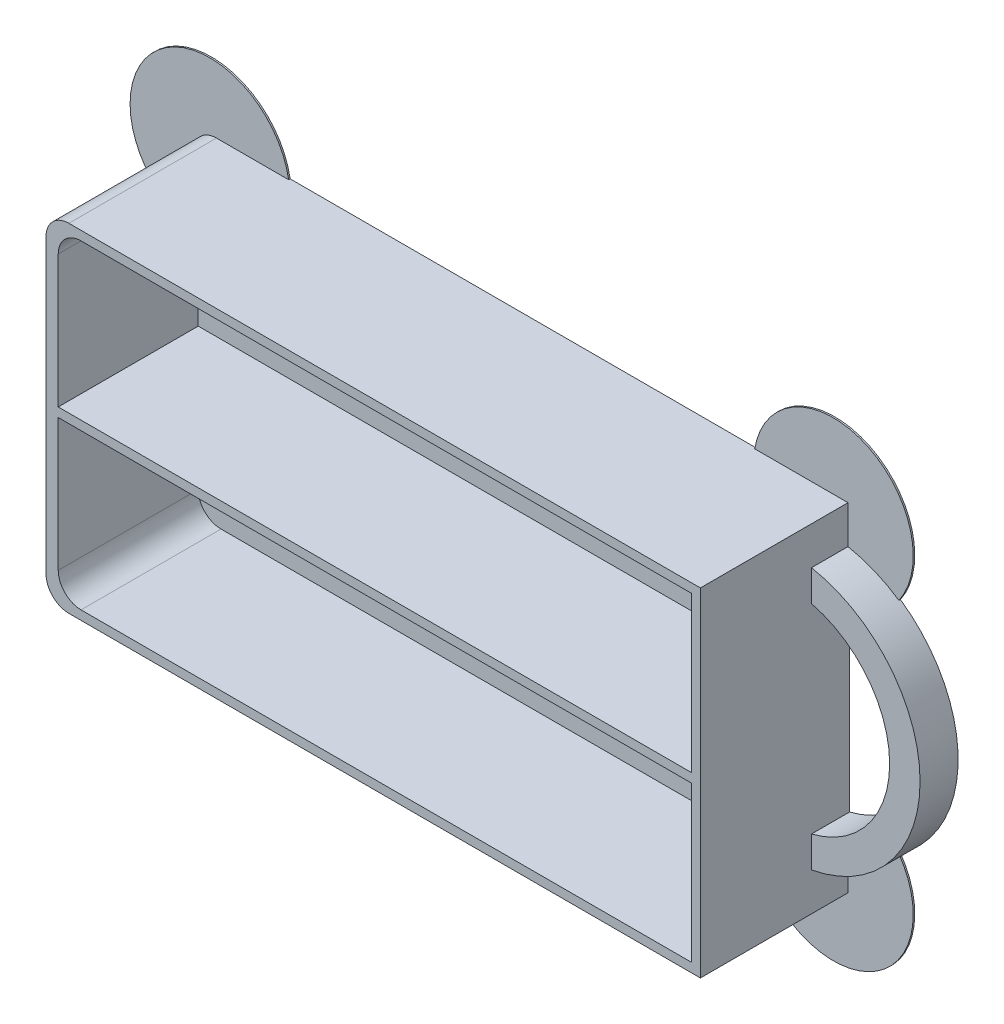
SolidWorks part; units mm, degrees
ref_plane "Спереди" through (0, 0, 0) normal (0, 0, 1) x (1, 0, 0)
ref_plane "Сверху" through (0, 0, 0) normal (0, 1, 0) x (1, 0, 0)
ref_plane "Справа" through (0, 0, 0) normal (1, 0, 0) x (0, 0, -1)
other "Configuration Table"
sketch "Эскиз1" plane through (0, 0, 0) normal (0, 0, 1) x (1, 0, 0)
  line L1 (-43, 22.2) -> (43, 22.2)
  line L2 (-43, 22.2) -> (-43, -22.2)
  line L3 (-43, -22.2) -> (43, -22.2)
  line L4 (43, 22.2) -> (43, -22.2)
  line L5 (-43, 22.2) -> (43, -22.2) construction
  line L6 (-43, -22.2) -> (43, 22.2) construction
  point P0 (0, 0)
  dimension "D1" = 86
  dimension "D2" = 44.4
extrude "Бобышка-Вытянуть1" add sketch "Эскиз1" along normal blind 19.6
sketch "Эскиз2" plane through (0, 0, 0) normal (0, 0, 1) x (1, 0, 0)
  line L0 (0, 0) -> (43, 0) construction
  line L1 (43, -22.2) -> (43, 22.2) construction
  line L2 (43, 17.2) -> (43, 13.1088)
  line L3 (43, -17.2) -> (43, -13.1088)
  arc A0 (43, -17.2) -> (43, 17.2) centre (39.7735, 0) ccw
  arc A1 (43, -13.1088) -> (43, 13.1088) centre (39.7735, 0) ccw
  dimension "D3" = 13.5
  dimension "D4" = 4
  dimension "D1" = 5
  dimension "D2" = 5
extrude "Бобышка-Вытянуть2" add sketch "Эскиз2" along normal blind 5
sketch "Эскиз3" plane through (0, 0, 19.6) normal (0, 0, 1) x (1, 0, 0)
  line L1 (41.8, 0.5971) -> (-41.4, 0.5971)
  line L2 (41.8, 0.5971) -> (41.8, -0.6029)
  line L3 (41.8, -0.6029) -> (-41.4, -0.6029)
  line L4 (-41.4, 0.5971) -> (-41.4, -0.6029)
  line L5 (-41.4, 22.2) -> (-41.4, -22.2)
  line L6 (-43, -21) -> (41.8, -21)
  line L7 (41.8, -21) -> (41.8, 21)
  line L8 (41.8, 21) -> (-43, 21)
  line L9 (-41.4, -21) -> (41.8, -21)
  line L10 (41.8, -21) -> (41.8, 21)
  line L11 (41.8, 21) -> (-41.4, 21)
  line L12 (-41.4, 21) -> (-41.4, -21)
  line L13 (41.8, 0.5971) -> (-41.4, -0.6029) construction
  line L14 (41.8, -0.6029) -> (-41.4, 0.5971) construction
  point P0 (0, 0)
  dimension "D3" = 1.2
  dimension "D4" = 20.4029
  dimension "D5" = 20.3971
  dimension "D1" = 1.2
  dimension "D2" = 1.6
extrude "Вырез-Вытянуть1" cut sketch "Эскиз3" against normal offset from surface (18.4 mm away) 1.2 contours L11 L12 L1 L10 | L3 L12 L9 L10 up to face at (48.1368, 0, 0)
fillet "Скругление1" radius 3 4 edges at (-43, 22.2, 9.8) (-43, -22.2, 9.8) (-41.4, -21, 10.4) (-41.4, 21, 10.4)
sketch "Эскиз4" plane through (0, 0, 0) normal (0, 0, -1) x (-1, 0, 0)
  line L0 (-43, 22.2) -> (40, 22.2) construction
  line L1 (43, 19.2) -> (43, -19.2) construction
  line L2 (-49.6891, 14.4198) -> (-30.7367, 22.2)
  line L3 (43, 10.1448) -> (30.5171, 22.2)
  line L4 (50, 0) -> (-50, 0) construction
  line L5 (43, -10.1448) -> (30.5171, -22.2)
  line L6 (-49.6891, -14.4198) -> (-30.7367, -22.2)
  arc A0 (-30.7367, 22.2) -> (-49.6891, 14.4198) centre (-41.0783, 20.4179) ccw
  arc A1 (-43, 17.2) -> (-43, -17.2) centre (-39.7735, 0) ccw construction
  arc A2 (30.5171, 22.2) -> (43, 10.1448) centre (40.8587, 20.4179) cw
  arc A3 (30.5171, -22.2) -> (43, -10.1448) centre (40.8587, -20.4179) ccw
  arc A4 (-30.7367, -22.2) -> (-49.6891, -14.4198) centre (-41.0783, -20.4179) cw
extrude "Бобышка-Вытянуть3" add sketch "Эскиз4" against normal blind 0.2
